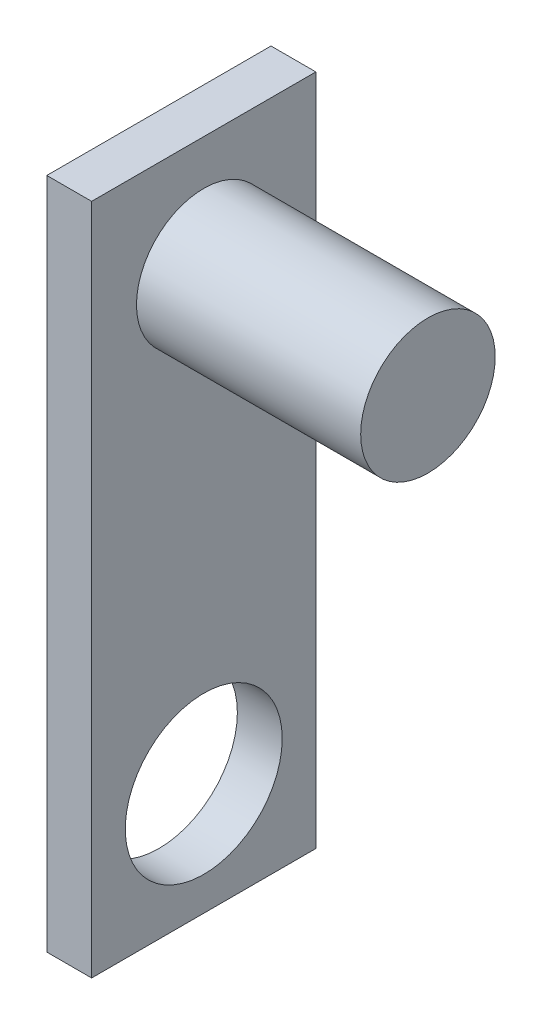
SolidWorks part; units mm, degrees
ref_plane "Front Plane" through (0, 0, 0) normal (0, 0, 1) x (1, 0, 0)
ref_plane "Top Plane" through (0, 0, 0) normal (0, 1, 0) x (1, 0, 0)
ref_plane "Right Plane" through (0, 0, 0) normal (1, 0, 0) x (0, 0, -1)
sketch "Sketch1" plane through (0, 0, 0) normal (1, 0, 0) x (0, 0, -1)
  line L1 (-5, -15) -> (5, -15)
  line L2 (-5, -15) -> (-5, 15)
  line L3 (-5, 15) -> (5, 15)
  line L4 (5, -15) -> (5, 15)
  line L5 (-5, -15) -> (5, 15) construction
  line L6 (-5, 15) -> (5, -15) construction
  point P0 (0, 0)
  dimension "D1" = 30
  dimension "D2" = 10
extrude "Boss-Extrude1" add sketch "Sketch1" along normal blind 2
sketch "Sketch2" plane through (2, 0, 0) normal (1, 0, 0) x (0, 0, -1)
  circle A0 centre (0, -10) radius 3.5
  dimension "D2" = 7
  dimension "D1" = 10
extrude "Cut-Extrude1" cut sketch "Sketch2" against normal up to surface (2 mm away) up to face at (0, 0, 0)
sketch "Sketch3" plane through (2, 0, 0) normal (1, 0, 0) x (0, 0, -1)
  circle A0 centre (0, 10) radius 3
  dimension "D1" = 10
extrude "Boss-Extrude2" add sketch "Sketch3" along normal blind 10
